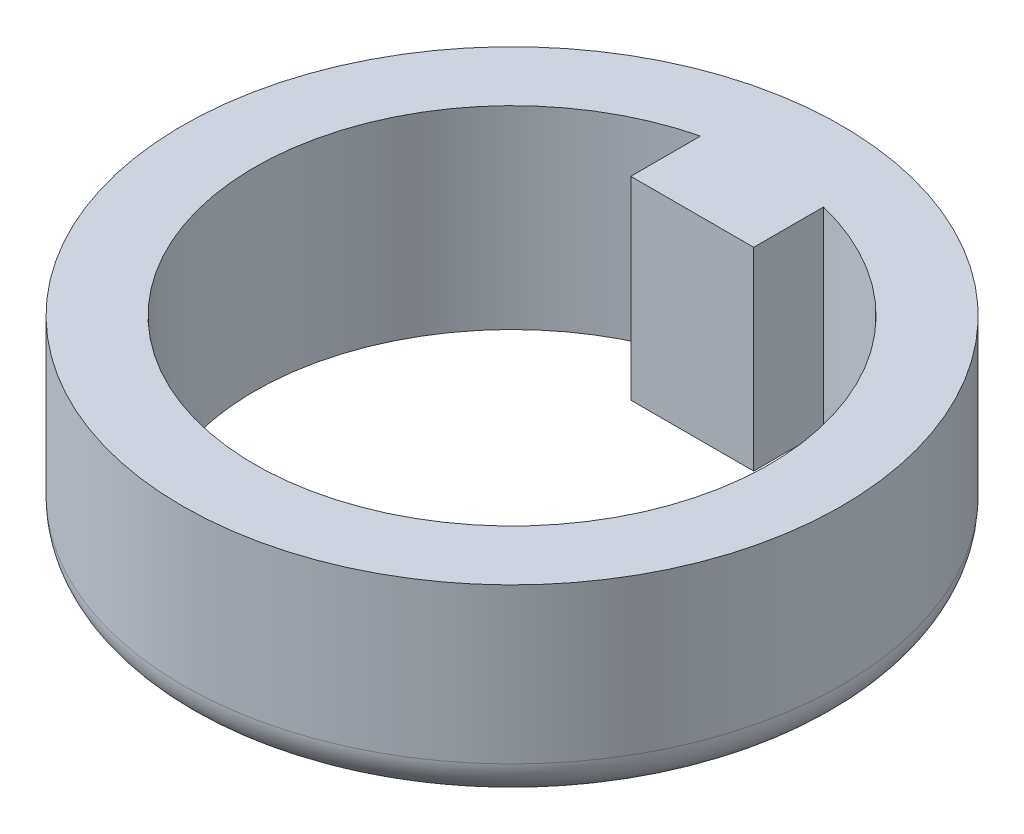
SolidWorks part; units mm, degrees
ref_plane "Front Plane" through (0, 0, 0) normal (0, 0, 1) x (1, 0, 0)
ref_plane "Top Plane" through (0, 0, 0) normal (0, 1, 0) x (1, 0, 0)
ref_plane "Right Plane" through (0, 0, 0) normal (1, 0, 0) x (0, 0, -1)
sketch "Sketch1" plane through (0, 0, 0) normal (0, 1, 0) x (1, 0, 0)
  line L0 (-1.585, 6.447) -> (-1.585, 4.647)
  line L1 (-1.585, 4.647) -> (1.585, 4.647)
  line L2 (1.585, 4.647) -> (1.585, 6.447)
  circle A0 centre (0, 0) radius 8.5
  arc A1 (-1.585, 6.447) -> (1.585, 6.447) centre (0, 0) ccw
  dimension "D1" = 13.278
  dimension "D2" = 17
  dimension "D3" = 1.8
  dimension "D4" = 3.17
  dimension "D5" = 1.585
extrude "Boss-Extrude1" add sketch "Sketch1" along normal blind 5
fillet "Fillet3" radius 1 1 edges at (0, 0, 8.5)
